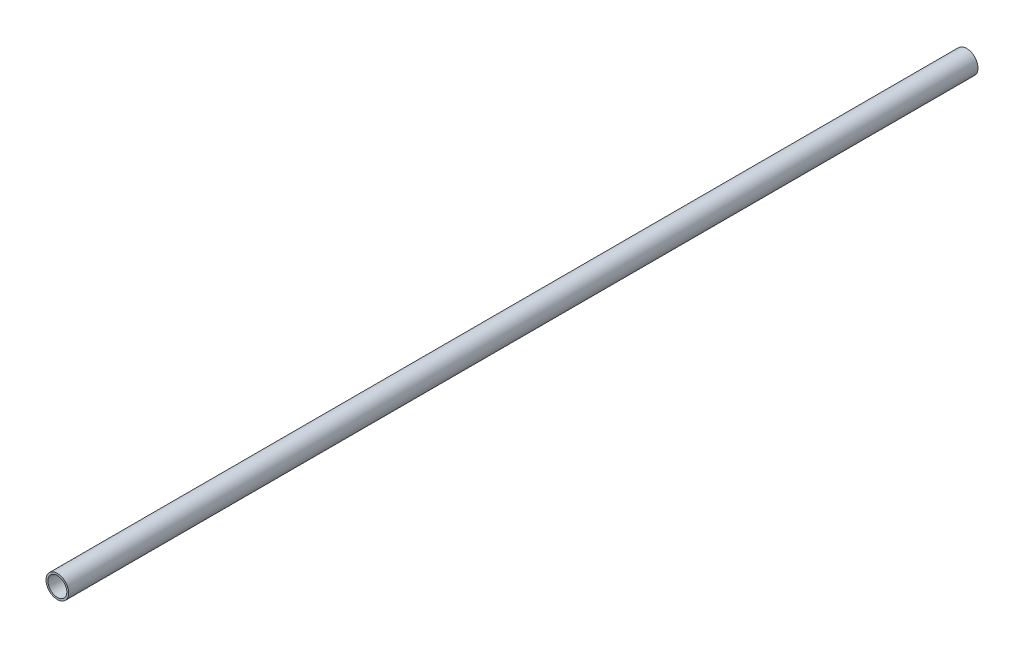
SolidWorks part; units mm, degrees
material "PVC Rigid"
ref_plane "Front Plane" through (0, 0, 0) normal (0, 0, 1) x (1, 0, 0)
ref_plane "Top Plane" through (0, 0, 0) normal (0, 1, 0) x (1, 0, 0)
ref_plane "Right Plane" through (0, 0, 0) normal (1, 0, 0) x (0, 0, -1)
sketch "Sketch1" plane through (0, 0, 0) normal (0, 0, 1) x (1, 0, 0)
  circle A0 centre (0, 0) radius 19.05
  circle A2 centre (0, 0) radius 15.875
  dimension "D1" = 38.1
  dimension "D2" = 31.75
extrude "Boss-Extrude1" add sketch "Sketch1" along normal blind 1524
